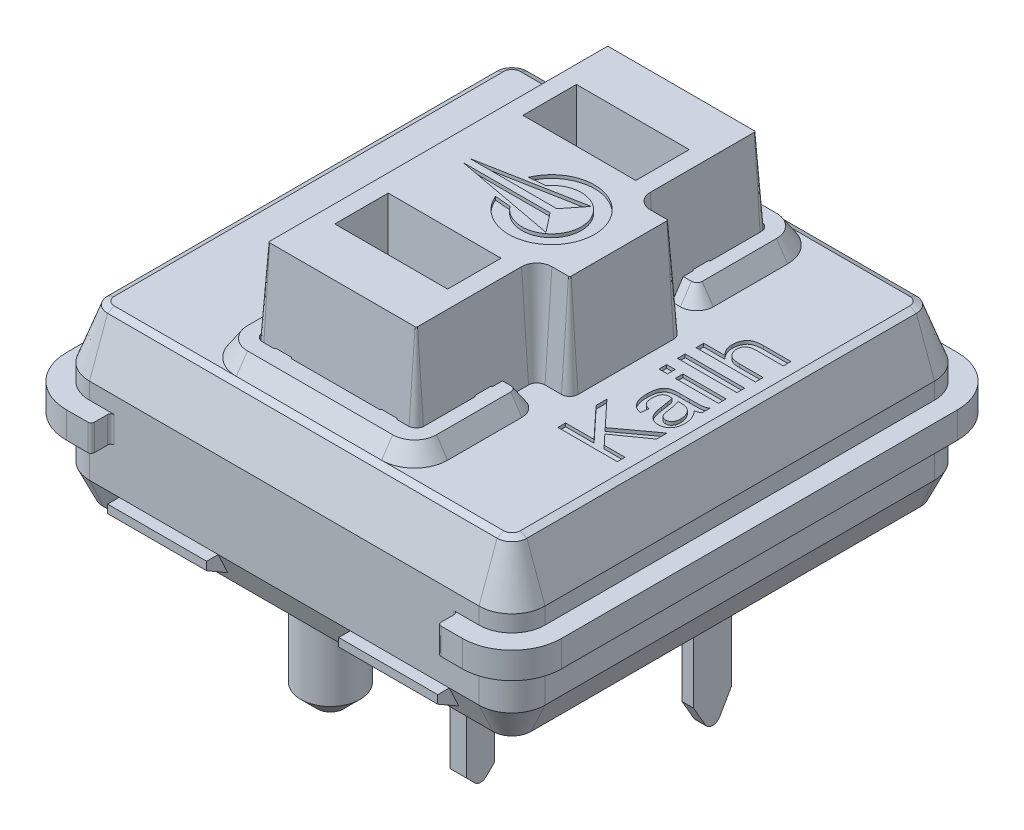
SolidWorks part; units mm, degrees
ref_plane "Front Plane" through (0, 0, 0) normal (0, 0, 1) x (1, 0, 0)
ref_plane "Top Plane" through (0, 0, 0) normal (0, 1, 0) x (1, 0, 0)
ref_plane "Right Plane" through (0, 0, 0) normal (1, 0, 0) x (0, 0, -1)
sketch "Sketch1" plane through (0, 0, 0) normal (0, 1, 0) x (1, 0, 0)
  line L0 (-12.6999, -17.2743) -> (27.7413, -17.2743) construction
  line L1 (-6, 7.5) -> (6, 7.5)
  line L2 (-7.5, 6) -> (-7.5, -6)
  line L3 (-6, -7.5) -> (6, -7.5)
  line L4 (7.5, 6) -> (7.5, -6)
  line L5 (-7.5, 7.5) -> (7.5, -7.5) construction
  line L6 (-7.5, -7.5) -> (7.5, 7.5) construction
  arc A0 (-7.5, -6) -> (-6, -7.5) centre (-6, -6) ccw
  arc A1 (6, -7.5) -> (7.5, -6) centre (6, -6) ccw
  arc A2 (6, 7.5) -> (7.5, 6) centre (6, 6) cw
  arc A3 (-6, 7.5) -> (-7.5, 6) centre (-6, 6) ccw
  point P0 (0, 0)
  dimension "D3" = 1.5
  dimension "D1" = 15
  dimension "D2" = 15
sketch "Sketch5" plane through (0, 0, 0) normal (0, 1, 0) x (1, 0, 0)
  line L1 (6, -7.5) -> (-6, -7.5)
  line L2 (7.5, -6) -> (7.5, 6)
  line L3 (6, 7.5) -> (-6, 7.5)
  line L4 (-7.5, -6) -> (-7.5, 6)
  line L5 (7.5, -7.5) -> (-7.5, 7.5) construction
  line L6 (7.5, 7.5) -> (-7.5, -7.5) construction
  arc A0 (-6, -7.5) -> (-7.5, -6) centre (-6, -6) cw
  arc A1 (6, -7.5) -> (7.5, -6) centre (6, -6) ccw
  arc A2 (7.5, 6) -> (6, 7.5) centre (6, 6) ccw
  arc A3 (-6, 7.5) -> (-7.5, 6) centre (-6, 6) ccw
  point P0 (0, 0)
  dimension "D1" = 1.5
extrude "Boss-Extrude4" add sketch "Sketch5" along normal mid plane 0.8
sketch "Sketch6" plane through (0, 0.4, 0) normal (0, 1, 0) x (1, 0, 0)
  line L0 (-7.5, 7.5) -> (7.5, -7.5) construction
  line L1 (5.9, -6.9) -> (-5.9, -6.9)
  line L2 (6.9, -5.9) -> (6.9, 5.9)
  line L3 (5.9, 6.9) -> (-5.9, 6.9)
  line L4 (-6.9, -5.9) -> (-6.9, 5.9)
  line L5 (6.9, -6.9) -> (-6.9, 6.9) construction
  line L6 (6.9, 6.9) -> (-6.9, -6.9) construction
  arc A0 (-5.9, -6.9) -> (-6.9, -5.9) centre (-5.9, -5.9) cw
  arc A1 (5.9, -6.9) -> (6.9, -5.9) centre (5.9, -5.9) ccw
  arc A2 (6.9, 5.9) -> (5.9, 6.9) centre (5.9, 5.9) ccw
  arc A3 (-5.9, 6.9) -> (-6.9, 5.9) centre (-5.9, 5.9) ccw
  point P0 (0, 0)
  dimension "D2" = 1
  dimension "D1" = 13.8
extrude "Boss-Extrude5" add sketch "Sketch6" along normal blind 0.5
sketch "Sketch7" plane through (0, 0.9, 0) normal (0, 1, 0) x (1, 0, 0)
  line L4 (-5.9, -6.9) -> (5.9, -6.9)
  line L5 (6.9, -5.9) -> (6.9, 5.9)
  line L6 (5.9, 6.9) -> (-5.9, 6.9)
  line L7 (-6.9, 5.9) -> (-6.9, -5.9)
  line L8 (-5.9, -6.9) -> (5.9, -6.9)
  line L9 (6.9, -5.9) -> (6.9, 5.9)
  line L10 (5.9, 6.9) -> (-5.9, 6.9)
  line L11 (-6.9, 5.9) -> (-6.9, -5.9)
  arc A4 (-6.9, -5.9) -> (-5.9, -6.9) centre (-5.9, -5.9) ccw
  arc A5 (5.9, -6.9) -> (6.9, -5.9) centre (5.9, -5.9) ccw
  arc A6 (6.9, 5.9) -> (5.9, 6.9) centre (5.9, 5.9) ccw
  arc A7 (-5.9, 6.9) -> (-6.9, 5.9) centre (-5.9, 5.9) ccw
  arc A8 (-6.9, -5.9) -> (-5.9, -6.9) centre (-5.9, -5.9) ccw
  arc A9 (5.9, -6.9) -> (6.9, -5.9) centre (5.9, -5.9) ccw
  arc A10 (6.9, 5.9) -> (5.9, 6.9) centre (5.9, 5.9) ccw
  arc A11 (-5.9, 6.9) -> (-6.9, 5.9) centre (-5.9, 5.9) ccw
  arc M9 (-6.9, -5.9) -> (-5.9, -6.9) centre (-5.9, -5.9) ccw
  line M10 (-5.9, -6.9) -> (5.9, -6.9)
  arc M11 (5.9, -6.9) -> (6.9, -5.9) centre (5.9, -5.9) ccw
  line M12 (6.9, -5.9) -> (6.9, 5.9)
  arc M13 (6.9, 5.9) -> (5.9, 6.9) centre (5.9, 5.9) ccw
  line M14 (5.9, 6.9) -> (-5.9, 6.9)
  arc M15 (-5.9, 6.9) -> (-6.9, 5.9) centre (-5.9, 5.9) ccw
  line M16 (-6.9, 5.9) -> (-6.9, -5.9)
  dimension "D1" = 0
extrude "Boss-Extrude6" add sketch "Sketch7" along normal offset from surface 2.5 draft 20 contours M16 M9 M10 M11 M12 M13 M14 M15
chamfer "Chamfer1" distance 0.1 angle 45 8 edges at (-6.1953, 2.5, -6.1953) (-6.3176, 2.5, 0) (-6.1953, 2.5, 6.1953) (0, 2.5, 6.3176) (6.1953, 2.5, 6.1953) (6.3176, 2.5, 0) (6.1953, 2.5, -6.1953) (0, 2.5, -6.3176)
sketch "Sketch8" plane through (0, 2.5, 0) normal (0, 1, 0) x (1, 0, 0)
  line L0 (5.9, 6.1503) -> (-5.9, 6.1503) construction
  line L1 (2.2, -6.1503) -> (-2.2, -6.1503)
  line L2 (3.2, -5.1503) -> (3.2, -2.9003)
  line L3 (2.2, 6.1503) -> (-2.2, 6.1503)
  line L4 (-3.2, -5.1503) -> (-3.2, 5.1503)
  line L5 (3.2, -6.1503) -> (-3.2, 6.1503) construction
  line L6 (3.2, 6.1503) -> (-3.2, -6.1503) construction
  line L7 (2.7, 2.4003) -> (2.3, 2.4003)
  line L8 (2.3, 2.4003) -> (2.3, -2.4003)
  line L9 (2.3, -2.4003) -> (2.7, -2.4003)
  line L10 (3.2, 2.9003) -> (3.2, 5.1503)
  arc A0 (-2.2, -6.1503) -> (-3.2, -5.1503) centre (-2.2, -5.1503) cw
  arc A1 (2.2, -6.1503) -> (3.2, -5.1503) centre (2.2, -5.1503) ccw
  arc A2 (3.2, 5.1503) -> (2.2, 6.1503) centre (2.2, 5.1503) ccw
  arc A3 (-2.2, 6.1503) -> (-3.2, 5.1503) centre (-2.2, 5.1503) ccw
  arc A4 (2.7, -2.4003) -> (3.2, -2.9003) centre (2.7, -2.9003) cw
  arc A5 (2.7, 2.4003) -> (3.2, 2.9003) centre (2.7, 2.9003) ccw
  point P0 (0, 0)
  point P28 (3.2, 2.4003)
  dimension "D2" = 1
  dimension "D5" = 0.5
  dimension "D1" = 6.4
  dimension "D3" = 3.75
  dimension "D4" = 0.9
extrude "Boss-Extrude7" add sketch "Sketch8" along normal blind 0.5 draft 34
sketch "Sketch9" plane through (0, 2.5, 0) normal (0, 1, 0) x (1, 0, 0)
  line L1 (-2.2, -5.35) -> (2.2, -5.35)
  line L2 (-2.45, -5.1) -> (-2.45, 5.1)
  line L3 (-2.2, 5.35) -> (2.2, 5.35)
  line L4 (2.45, -5.1) -> (2.45, 5.1)
  line L5 (-2.45, -5.35) -> (2.45, 5.35) construction
  line L6 (-2.45, 5.35) -> (2.45, -5.35) construction
  arc A0 (-2.2, -5.35) -> (-2.45, -5.1) centre (-2.2, -5.1) cw
  arc A1 (2.2, -5.35) -> (2.45, -5.1) centre (2.2, -5.1) ccw
  arc A2 (2.2, 5.35) -> (2.45, 5.1) centre (2.2, 5.1) cw
  arc A3 (-2.45, 5.1) -> (-2.2, 5.35) centre (-2.2, 5.1) cw
  point P0 (0, 0)
  dimension "D2" = 0.25
  dimension "D1" = 10.7
  dimension "D3" = 4.9
extrude "Cut-Extrude1" cut sketch "Sketch9" along normal through all
sketch "Sketch11" plane through (0, 2.5, 0) normal (0, 1, 0) x (1, 0, 0)
  line L0 (2.2, 5.35) -> (-2.2, 5.35) construction
  line L1 (2.45, 2.7376) -> (2.45, 5.1) construction
  line L2 (-2.45, 5.1) -> (-2.45, -5.1) construction
  line L3 (-2.2, -5.35) -> (2.2, -5.35) construction
  line L4 (2.45, -5.1) -> (2.45, -2.7376) construction
  line L5 (-1.8598, 5.35) -> (-1.3402, 5.35)
  line L6 (1.3402, 5.35) -> (1.8598, 5.35)
  line L7 (2.45, 3.5598) -> (2.45, 3.0402)
  line L8 (2.45, -3.0402) -> (2.45, -3.5598)
  line L9 (1.8598, -5.35) -> (1.3402, -5.35)
  line L10 (-1.3402, -5.35) -> (-1.8598, -5.35)
  line L11 (-2.45, -3.5598) -> (-2.45, -3.0402)
  line L12 (-2.45, 3.0402) -> (-2.45, 3.5598)
  line L13 (0, 0) -> (-1.4423, 0) construction
  line L14 (0, 0) -> (0, 1.7321) construction
  arc A0 (-1.8598, 5.35) -> (-1.3402, 5.35) centre (-1.6, 5.5) ccw
  arc A1 (1.3402, 5.35) -> (1.8598, 5.35) centre (1.6, 5.5) ccw
  arc A2 (2.45, 3.5598) -> (2.45, 3.0402) centre (2.6, 3.3) ccw
  arc A3 (-2.45, 3.5598) -> (-2.45, 3.0402) centre (-2.6, 3.3) cw
  arc A4 (-2.45, -3.0402) -> (-2.45, -3.5598) centre (-2.6, -3.3) cw
  arc A5 (-1.8598, -5.35) -> (-1.3402, -5.35) centre (-1.6, -5.5) cw
  arc A6 (1.3402, -5.35) -> (1.8598, -5.35) centre (1.6, -5.5) cw
  arc A7 (2.45, -3.0402) -> (2.45, -3.5598) centre (2.6, -3.3) ccw
  point P32 (2.45, 3.3)
  point P38 (-2.3, 3.3)
  dimension "D1" = 0.3
  dimension "D2" = 0.15
  dimension "D3" = 1.6
  dimension "D4" = 3.3
extrude "Boss-Extrude8" add sketch "Sketch11" along normal up to surface (0.5 mm away) up to face at (0.7315, 3, 0)
sketch "Sketch12" plane through (0, 2.5, 0) normal (0, 1, 0) x (1, 0, 0)
  line L0 (2.7, 1.7) -> (3.2, 1.7)
  line L1 (2.2, 5.35) -> (-2.2, 5.35)
  line L2 (2.45, 5.1) -> (2.45, 1.95)
  line L3 (2.2, -5.35) -> (-2.2, -5.35)
  line L4 (-2.45, 5.1) -> (-2.45, -5.1)
  line L5 (2.45, 5.35) -> (-2.45, -5.35) construction
  line L6 (2.45, -5.35) -> (-2.45, 5.35) construction
  line L7 (3.45, 1.45) -> (3.45, -1.45)
  line L8 (3.2, -1.7) -> (2.7, -1.7)
  line L9 (2.45, -1.95) -> (2.45, -5.1)
  line L10 (-1.5, -2.25) -> (1.5, -3.45) construction
  line L11 (-1.5, -2.25) -> (1.5, -2.25)
  line L12 (-1.5, -2.25) -> (-1.5, -3.45)
  line L13 (-1.5, -3.45) -> (1.5, -3.45)
  line L14 (1.5, -2.25) -> (1.5, -3.45)
  line L15 (0, 0) -> (-1.3542, 0) construction
  line L16 (1.5, 2.25) -> (1.5, 3.45)
  line L17 (-1.5, 3.45) -> (1.5, 3.45)
  line L18 (-1.5, 2.25) -> (-1.5, 3.45)
  line L19 (-1.5, 2.25) -> (1.5, 2.25)
  arc A0 (-2.2, -5.35) -> (-2.45, -5.1) centre (-2.2, -5.1) cw
  arc A1 (2.45, -5.1) -> (2.2, -5.35) centre (2.2, -5.1) cw
  arc A2 (2.7, -1.7) -> (2.45, -1.95) centre (2.7, -1.95) ccw
  arc A3 (-2.2, 5.35) -> (-2.45, 5.1) centre (-2.2, 5.1) ccw
  arc A4 (2.2, 5.35) -> (2.45, 5.1) centre (2.2, 5.1) cw
  arc A5 (2.7, 1.7) -> (2.45, 1.95) centre (2.7, 1.95) cw
  arc A6 (3.2, 1.7) -> (3.45, 1.45) centre (3.2, 1.45) cw
  arc A7 (3.45, -1.45) -> (3.2, -1.7) centre (3.2, -1.45) cw
  point P0 (0, 0)
  point P18 (2.45, -1.7)
  point P29 (3.45, 1.7)
  point P32 (3.45, -1.7)
  point P37 (0, -2.85)
  point P38 (0, 0)
  dimension "D5" = 0.25
  dimension "D1" = 4.9
  dimension "D2" = 10.7
  dimension "D3" = 1
  dimension "D4" = 3.4
  dimension "D6" = 1.2
  dimension "D7" = 3
  dimension "D8" = 5.7
extrude "Boss-Extrude9" add sketch "Sketch12" along normal blind 3 draft 4
sketch "Sketch13" plane through (0, 2.5, 0) normal (0, 1, 0) x (1, 0, 0)
  line L0 (5.809, 2.994) -> (5.809, -2.994) construction
  line L1 (5.809, 0) -> (0, 0) construction
  text T0 "Kailh" font "@Arial Unicode MS" height 1.8
extrude "Cut-Extrude2" cut sketch "Sketch13" against normal blind 0.1
sketch "Sketch14" plane through (0, 5.5, 0) normal (0, 1, 0) x (1, 0, 0)
  line L0 (0, 0.5) -> (0.4816, 0.5421)
  line L1 (0, -0.5) -> (0.4816, -0.5421)
  line L2 (0, 0) -> (-1.6937, 0) construction
  line L3 (-1.377, 0.1043) -> (1.2556, 0.1043)
  line L4 (1.2556, 0.1043) -> (1.7122, 0.6819)
  line L5 (1.7122, 0.6819) -> (-1.377, 0.1043)
  line L6 (1.2556, -0.1043) -> (1.7122, -0.6819)
  line L7 (-1.377, -0.1043) -> (1.2556, -0.1043)
  line L8 (1.7122, -0.6819) -> (-1.377, -0.1043)
  arc A0 (0, -0.5) -> (0, 0.5) centre (1.2, 0) ccw
  arc A1 (0.4816, -0.5421) -> (0.4816, 0.5421) centre (1.2, 0) ccw
  point P1 (1.2556, 0.1043)
  point P12 (1.7122, 0.6819)
  dimension "D2" = 0.9
  dimension "D3" = 1.3
  dimension "D1" = 10
  dimension "D4" = 1.2
  dimension "D5" = 1
extrude "Cut-Extrude3" cut sketch "Sketch14" against normal blind 0.1
sketch "Sketch15" plane through (0, 0, 0) normal (0, 1, 0) x (1, 0, 0)
  line L0 (22.7981, 9.2794) -> (-33.7496, 9.2794) construction
sketch "Sketch16" plane through (0, -0.4, 0) normal (0, -1, 0) x (1, 0, 0)
  line L1 (5.9, -6.9) -> (-5.9, -6.9)
  line L2 (6.9, -5.9) -> (6.9, 5.9)
  line L3 (5.9, 6.9) -> (-5.9, 6.9)
  line L4 (-6.9, -5.9) -> (-6.9, 5.9)
  line L5 (6.9, -6.9) -> (-6.9, 6.9) construction
  line L6 (6.9, 6.9) -> (-6.9, -6.9) construction
  arc A0 (-5.9, -6.9) -> (-6.9, -5.9) centre (-5.9, -5.9) cw
  arc A1 (5.9, -6.9) -> (6.9, -5.9) centre (5.9, -5.9) ccw
  arc A2 (6.9, 5.9) -> (5.9, 6.9) centre (5.9, 5.9) ccw
  arc A3 (-6.9, 5.9) -> (-5.9, 6.9) centre (-5.9, 5.9) cw
  point P0 (0, 0)
  dimension "D2" = 1
  dimension "D1" = 13.8
extrude "Boss-Extrude10" add sketch "Sketch16" along normal blind 1.3
sketch "Sketch17" plane through (0, -1.7, 0) normal (0, -1, 0) x (1, 0, 0)
  line L4 (-5.9, -6.9) -> (5.9, -6.9)
  line L5 (6.9, -5.9) -> (6.9, 5.9)
  line L6 (5.9, 6.9) -> (-5.9, 6.9)
  line L7 (-6.9, 5.9) -> (-6.9, -5.9)
  line L8 (-5.9, -6.9) -> (5.9, -6.9)
  line L9 (6.9, -5.9) -> (6.9, 5.9)
  line L10 (5.9, 6.9) -> (-5.9, 6.9)
  line L11 (-6.9, 5.9) -> (-6.9, -5.9)
  arc A4 (-6.9, -5.9) -> (-5.9, -6.9) centre (-5.9, -5.9) ccw
  arc A5 (5.9, -6.9) -> (6.9, -5.9) centre (5.9, -5.9) ccw
  arc A6 (6.9, 5.9) -> (5.9, 6.9) centre (5.9, 5.9) ccw
  arc A7 (-5.9, 6.9) -> (-6.9, 5.9) centre (-5.9, 5.9) ccw
  arc A8 (-6.9, -5.9) -> (-5.9, -6.9) centre (-5.9, -5.9) ccw
  arc A9 (5.9, -6.9) -> (6.9, -5.9) centre (5.9, -5.9) ccw
  arc A10 (6.9, 5.9) -> (5.9, 6.9) centre (5.9, 5.9) ccw
  arc A11 (-5.9, 6.9) -> (-6.9, 5.9) centre (-5.9, 5.9) ccw
  dimension "D1" = 0
extrude "Boss-Extrude11" add sketch "Sketch17" along normal blind 0.9 draft 25
sketch "Sketch18" plane through (0, -2.6, 0) normal (0, -1, 0) x (1, 0, 0)
  line L1 (-6.275, 2.5) -> (-3.125, 2.5)
  line L2 (-6.275, 2.5) -> (-6.275, -2.5)
  line L3 (-6.275, -2.5) -> (-3.125, -2.5)
  line L4 (-3.125, 2.5) -> (-3.125, -2.5)
  line L5 (-6.275, 2.5) -> (-3.125, -2.5) construction
  line L6 (-6.275, -2.5) -> (-3.125, 2.5) construction
  point P0 (-4.7, 0)
  point P5 (0, 0)
  dimension "D1" = 3.15
  dimension "D2" = 5
  dimension "D3" = 4.7
extrude "Cut-Extrude4" cut sketch "Sketch18" against normal blind 4
sketch "Sketch19" plane through (0, -2.6, 0) normal (0, -1, 0) x (1, 0, 0)
  line L0 (0, 0) -> (2.7131, 0) construction
  circle A0 centre (0, 0) radius 1.6
  circle A1 centre (0, 5.5) radius 0.9
  circle A3 centre (0, -5.5) radius 0.9
  dimension "D1" = 3.2
  dimension "D3" = 1.8
  dimension "D2" = 11
extrude "Boss-Extrude12" add sketch "Sketch19" along normal blind 2.65
chamfer "Chamfer2" distance 0.5 angle 45 3 edges at (0, -5.25, -4.6) (0, -5.25, -1.6) (0, -5.25, 4.6)
sketch "Sketch20" plane through (0, -2.6, 0) normal (0, -1, 0) x (1, 0, 0)
  line L1 (5.725, 0.575) -> (6.075, 0.575)
  line L2 (5.725, 0.575) -> (5.725, -0.575)
  line L3 (5.725, -0.575) -> (6.075, -0.575)
  line L4 (6.075, 0.575) -> (6.075, -0.575)
  line L5 (5.725, 0.575) -> (6.075, -0.575) construction
  line L6 (5.725, -0.575) -> (6.075, 0.575) construction
  line L8 (3.55, 5.425) -> (4.05, 5.425)
  line L9 (3.55, 5.425) -> (3.55, 4.575)
  line L10 (3.55, 4.575) -> (4.05, 4.575)
  line L11 (4.05, 5.425) -> (4.05, 4.575)
  line L12 (3.55, 5.425) -> (4.05, 4.575) construction
  line L13 (3.55, 4.575) -> (4.05, 5.425) construction
  point P0 (5.9, 0)
  point P5 (3.8, 5)
  dimension "D1" = 1.15
  dimension "D2" = 0.35
  dimension "D3" = 5.9
  dimension "D4" = 0.5
  dimension "D5" = 0.85
  dimension "D6" = 5
  dimension "D7" = 3.8
extrude "Boss-Extrude13" add sketch "Sketch20" along normal blind 3
sketch "Sketch21" plane through (6.075, 0, 0) normal (1, 0, 0) x (0, 0, -1)
  line L0 (0, -5.6) -> (0, -3.8431) construction
  line L1 (0.575, -5.6) -> (-0.575, -5.6) construction
  line L2 (-5, -5.6) -> (-5, -3.8431) construction
  line L3 (-4.575, -5.6) -> (-5.425, -5.6) construction
  line L4 (-0.575, -4.8541) -> (-0.2165, -5.475)
  line L5 (-0.575, -5.6) -> (-0.575, -2.6) construction
  line L6 (0.575, -4.8541) -> (0.2165, -5.475)
  line L7 (0.575, -5.6) -> (0.575, -2.6) construction
  line L8 (-5.425, -5.2786) -> (-5.1768, -5.5268)
  line L9 (-5.425, -5.6) -> (-5.425, -2.6) construction
  line L10 (-4.575, -5.2786) -> (-4.8232, -5.5268)
  line L11 (-4.575, -5.6) -> (-4.575, -2.6) construction
  line L12 (-0.575, -4.8541) -> (-0.575, -5.7)
  line L13 (-0.575, -5.7) -> (-4.575, -5.7)
  line L14 (-4.575, -5.7) -> (-4.575, -5.2786)
  line L16 (-5.425, -5.2786) -> (-5.425, -6.7)
  line L17 (-5.425, -6.7) -> (0.575, -6.7)
  line L18 (0.575, -6.7) -> (0.575, -4.8541)
  arc A0 (-0.2165, -5.475) -> (0.2165, -5.475) centre (0, -5.35) ccw
  arc A1 (-5.1768, -5.5268) -> (-4.8232, -5.5268) centre (-5, -5.35) ccw
  dimension "D1" = 0.5
  dimension "D2" = 30
  dimension "D3" = 45
  dimension "D4" = 0.1
  dimension "D5" = 1
extrude "Cut-Extrude5" cut sketch "Sketch21" against normal up to surface (2.525 mm away) up to face at (3.55, -4.1, 5)
sketch "Sketch22" plane through (0, 0, 0) normal (1, 0, 0) x (0, 0, -1)
  line L0 (-13.7977, 33.6254) -> (-14.1977, -19.6321) construction
  line L1 (-6.9, -1.7) -> (-7.25, -1.7)
  line L2 (-7.25, -1.7) -> (-7.25, -1.95)
  line L3 (-7.25, -1.95) -> (-6.6115, -2.3186)
  line L4 (-6.4803, -2.6) -> (-6.9, -1.7) construction
  line L5 (-6.6115, -2.3186) -> (-6.9, -1.7)
  line L6 (0, 0) -> (0, -3.4947) construction
  dimension "D1" = 14.5
  dimension "D2" = 30
  dimension "D3" = 0.25
extrude "Boss-Extrude14" add sketch "Sketch22" along normal blind 3 from offset 2
mirror "Mirror1" about plane through (0, 0, 0) normal (1, 0, 0) of "Boss-Extrude14"
mirror "Mirror2" about plane through (0, 0, 0) normal (0, 0, 1) of "Mirror1", "Boss-Extrude14"
sketch "Sketch23" plane through (0, -0.4, 0) normal (0, -1, 0) x (1, 0, 0)
  line L0 (-6, 7.5) -> (6, 7.5) construction
  line L1 (-5.25, 7.5) -> (5.25, 7.5)
  line L2 (-5.25, 7.5) -> (-5.25, 6.9)
  line L3 (-5.25, 6.9) -> (5.25, 6.9)
  line L4 (5.25, 7.5) -> (5.25, 6.9)
  line L5 (5.9, 6.9) -> (5, 6.9) construction
  line L6 (0, 0) -> (0, 6.9) construction
  line L7 (2, 6.9) -> (-2, 6.9) construction
  line L8 (0, 0) -> (-4.2254, 0) construction
  line L9 (5.25, -7.5) -> (5.25, -6.9)
  line L10 (-5.25, -6.9) -> (5.25, -6.9)
  line L11 (-5.25, -7.5) -> (-5.25, -6.9)
  line L12 (-5.25, -7.5) -> (5.25, -7.5)
  dimension "D1" = 10.5
extrude "Cut-Extrude6" cut sketch "Sketch23" against normal up to next
fillet "Fillet1" radius 0.1 8 edges at (-5.25, 0, 6.9) (5.25, 0, 6.9) (5.25, 0, -6.9) (-5.25, 0, -6.9) (-5.25, 0, -7.5) (5.25, 0, -7.5) (5.25, 0, 7.5) (-5.25, 0, 7.5)
